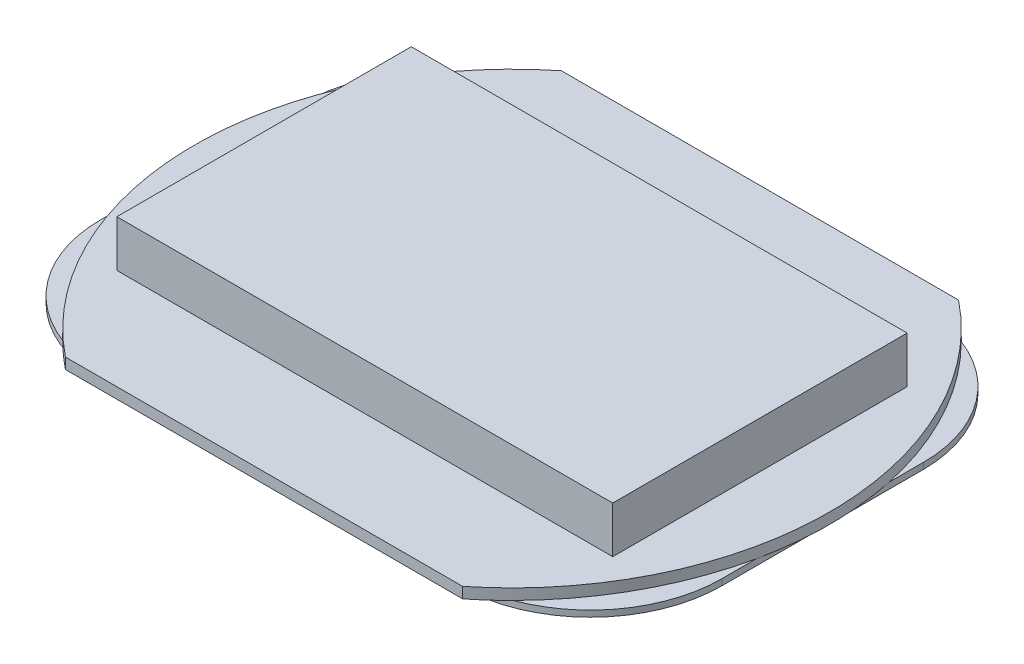
SolidWorks part; units mm, degrees
ref_plane "Спереди" through (0, 0, 0) normal (0, 0, 1) x (1, 0, 0)
ref_plane "Сверху" through (0, 0, 0) normal (0, 1, 0) x (1, 0, 0)
ref_plane "Справа" through (0, 0, 0) normal (1, 0, 0) x (0, 0, -1)
sketch "Эскиз1" plane through (0, 0, 0) normal (0, 1, 0) x (1, 0, 0)
  line L0 (-12.816, 16) -> (12.816, 16)
  line L3 (-12.816, -16) -> (12.816, -16)
  line L4 (-20.5, 16) -> (20.5, -16) construction
  line L5 (20.5, 16) -> (-20.5, -16) construction
  circle A0 centre (0, 0) radius 20.5 construction
  arc A1 (12.816, -16) -> (12.816, 16) centre (0, 0) ccw
  arc A2 (-12.816, -16) -> (-12.816, 16) centre (0, 0) cw
  point P1 (0, 0)
extrude "Бобышка-Вытянуть1" add sketch "Эскиз1" along normal blind 0.7
sketch "Эскиз2" plane through (0, 0, 0) normal (0, -1, 0) x (1, 0, 0)
  line L0 (-11.55, 15) -> (11.55, 15)
  line L1 (-20.05, 6.5) -> (-20.05, -6.5)
  line L2 (20.05, 6.5) -> (20.05, -6.5)
  line L3 (-11.55, -15) -> (11.55, -15)
  line L4 (-20.05, 15) -> (20.05, -15) construction
  line L5 (20.05, 15) -> (-20.05, -15) construction
  line L6 (-11, 5.5) -> (11, 5.5)
  line L7 (-11, 5.5) -> (-11, -5.5)
  line L8 (11, 5.5) -> (11, -5.5)
  line L9 (-11, -5.5) -> (11, -5.5)
  line L10 (-11, 5.5) -> (11, -5.5) construction
  line L11 (11, 5.5) -> (-11, -5.5) construction
  circle A0 centre (-20.05, 15) radius 8.5 construction
  circle A1 centre (-20.05, -15) radius 8.5 construction
  circle A2 centre (20.05, 15) radius 8.5 construction
  circle A3 centre (20.05, -15) radius 8.5 construction
  arc A4 (-11.55, 15) -> (-20.05, 6.5) centre (-11.55, 6.5) ccw
  arc A5 (-20.05, -6.5) -> (-11.55, -15) centre (-11.55, -6.5) ccw
  arc A6 (11.55, -15) -> (20.05, -6.5) centre (11.55, -6.5) ccw
  arc A7 (11.55, 15) -> (20.05, 6.5) centre (11.55, 6.5) cw
  point P1 (0, 0)
  point P23 (0, 0)
extrude "Бобышка-Вытянуть2" add sketch "Эскиз2" along normal blind 0.4
sketch "Эскиз3" plane through (0, 0.7, 0) normal (0, 1, 0) x (1, 0, 0)
  line L0 (-16, 9.5) -> (16, 9.5)
  line L1 (-16, 9.5) -> (-16, -9.5)
  line L2 (16, 9.5) -> (16, -9.5)
  line L3 (-16, -9.5) -> (16, -9.5)
  line L4 (-16, 9.5) -> (16, -9.5) construction
  line L5 (16, 9.5) -> (-16, -9.5) construction
  point P1 (0, 0)
extrude "Бобышка-Вытянуть3" add sketch "Эскиз3" along normal blind 3
